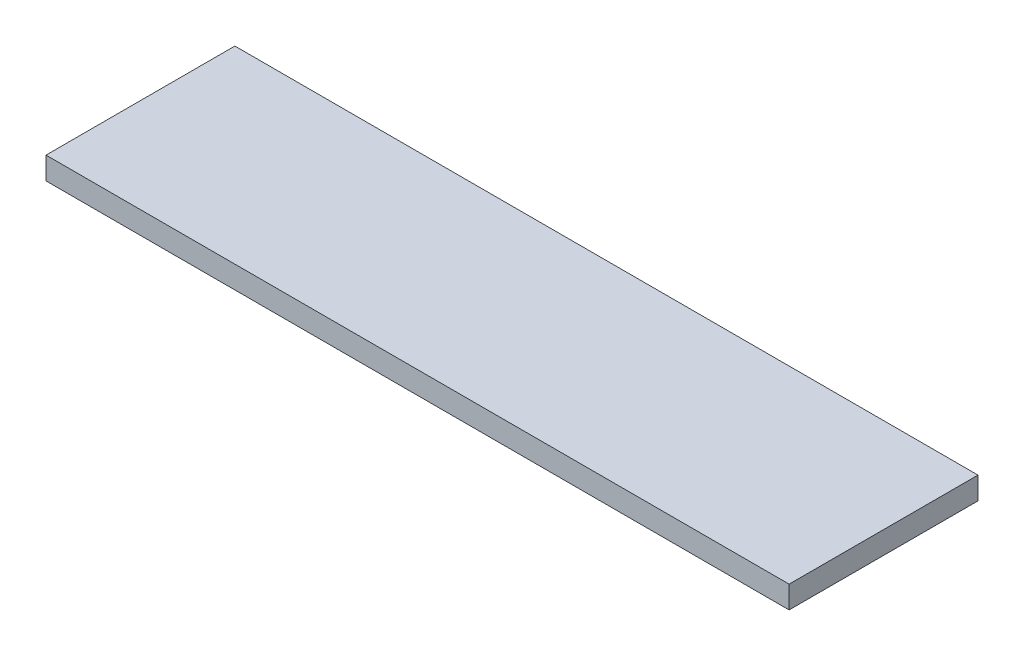
SolidWorks part; units mm, degrees
ref_plane "Спереди" through (0, 0, 0) normal (0, 0, 1) x (1, 0, 0)
ref_plane "Сверху" through (0, 0, 0) normal (0, 1, 0) x (1, 0, 0)
ref_plane "Справа" through (0, 0, 0) normal (1, 0, 0) x (0, 0, -1)
sketch "Эскиз1" plane through (0, 0, 0) normal (0, 1, 0) x (1, 0, 0)
  line L1 (299, -76) -> (-299, -76)
  line L2 (299, -76) -> (299, 76)
  line L3 (299, 76) -> (-299, 76)
  line L4 (-299, -76) -> (-299, 76)
  line L5 (299, -76) -> (-299, 76) construction
  line L6 (299, 76) -> (-299, -76) construction
  point P0 (0, 0)
  dimension "D1" = 152
  dimension "D2" = 598
extrude "Бобышка-Вытянуть1" add sketch "Эскиз1" along normal blind 18
